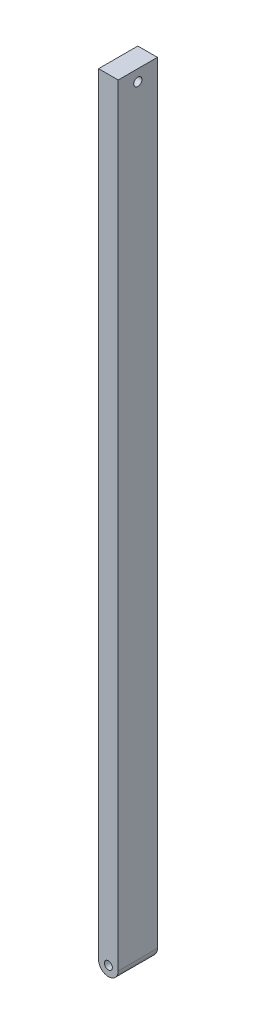
SolidWorks part; units mm, degrees
ref_plane "Front Plane" through (0, 0, 0) normal (0, 0, 1) x (1, 0, 0)
ref_plane "Top Plane" through (0, 0, 0) normal (0, 1, 0) x (1, 0, 0)
ref_plane "Right Plane" through (0, 0, 0) normal (1, 0, 0) x (0, 0, -1)
sketch "Sketch5" plane through (0, 0, 0) normal (0, 0, 1) x (1, 0, 0)
  line L0 (-1, -2.148) -> (-1, -40.898)
  line L1 (0, -2.148) -> (0, -40.898)
  line L2 (-1, -2.148) -> (-1, -1.568)
  line L3 (-1, -1.568) -> (0, -1.568)
  line L4 (0, -1.568) -> (0, -2.148)
  line L5 (-1, -2.148) -> (0, -2.148) construction
  arc A1 (-1, -40.898) -> (0, -40.898) centre (-0.5, -40.898) ccw
  circle A3 centre (-0.5, -40.898) radius 0.2039
  dimension "D1" = 1
  dimension "D2" = 38.75
  dimension "D3" = 0.58
extrude "Boss-Extrude2" add sketch "Sketch5" along normal blind 2
sketch "Sketch7" plane through (0, 0, 0) normal (1, 0, 0) x (0, 0, -1)
  line L0 (-2, -1.568) -> (-2, -2.148) construction
  line L1 (-2, -40.898) -> (-2, -1.568) construction
  line L2 (-2, -2.148) -> (0, -2.148) construction
  line L3 (0, -40.898) -> (0, -1.568) construction
  circle A0 centre (-1, -2.148) radius 0.2088
  dimension "D1" = 0.58
extrude "Cut-Extrude5" cut sketch "Sketch7" against normal through all
